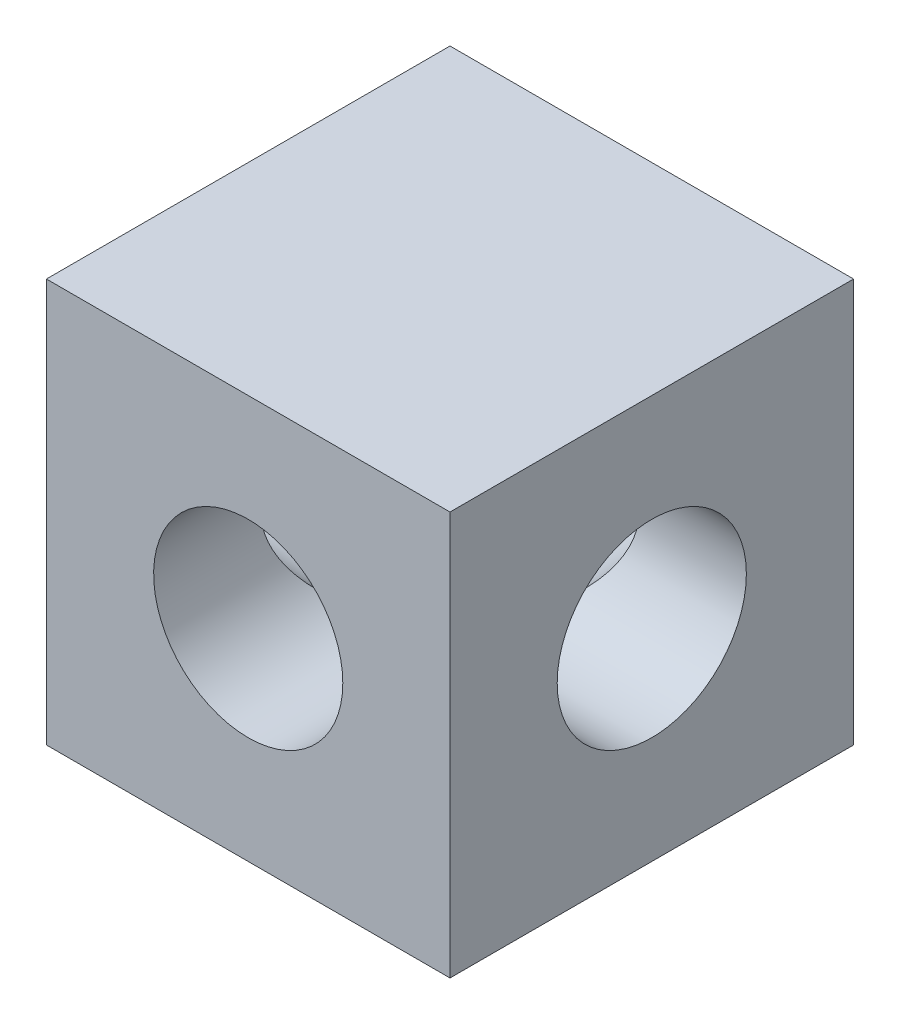
SolidWorks part; units mm, degrees
ref_plane "Front" through (0, 0, 0) normal (0, 0, 1) x (1, 0, 0)
ref_plane "Top" through (0, 0, 0) normal (0, 1, 0) x (-1, 0, 0)
ref_plane "Right" through (0, 0, 0) normal (1, 0, 0) x (0, 0, -1)
sketch "Sketch1" plane through (0, 0, 0) normal (0, 0, 1) x (1, 0, 0)
  line L0 (-10.16, -10.16) -> (10.16, -10.16)
  line L1 (-10.16, -10.16) -> (-10.16, 10.16)
  line L2 (10.16, 10.16) -> (-10.16, 10.16)
  line L3 (10.16, 10.16) -> (10.16, -10.16)
  line L4 (10.16, 10.16) -> (-10.16, -10.16) construction
  circle A0 centre (0, 0) radius 4.7625
  dimension "D1" = 20.32
  dimension "D2" = 20.32
extrude "Base-Extrude" add sketch "Sketch1" along normal mid plane 20.32
sketch "Sketch3" plane through (10.16, 0, 0) normal (1, 0, 0) x (0, 0, -1)
  circle A0 centre (0, 0) radius 4.7625
extrude "Cut-Extrude1" cut sketch "Sketch3" against normal through all
